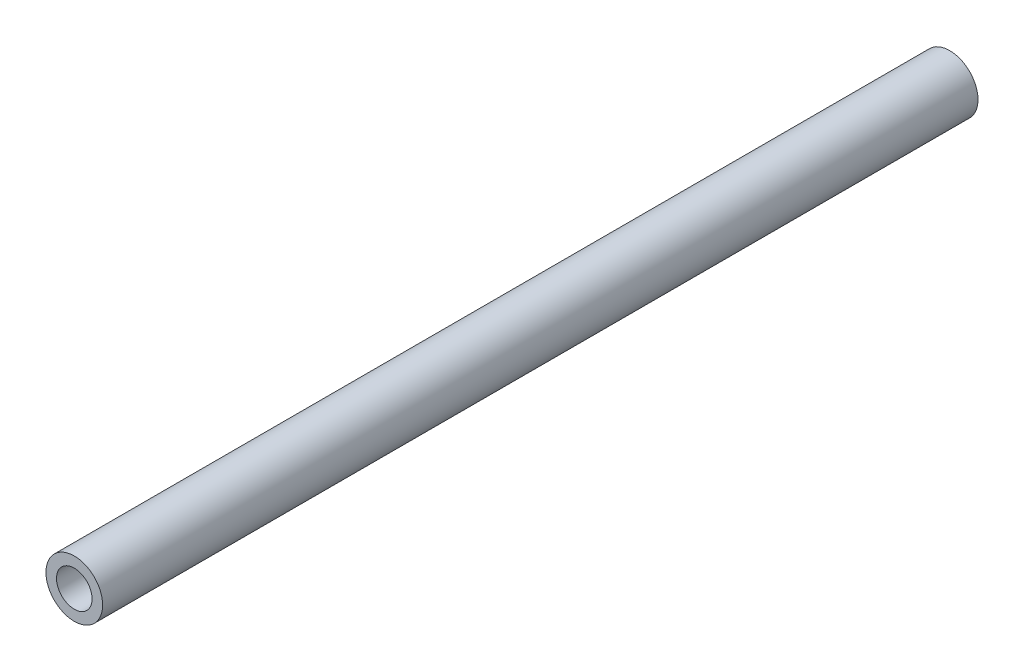
SolidWorks part; units mm, degrees
ref_plane "Plan de face" through (0, 0, 0) normal (0, 0, 1) x (1, 0, 0)
ref_plane "Plan de dessus" through (0, 0, 0) normal (0, 1, 0) x (1, 0, 0)
ref_plane "Plan de droite" through (0, 0, 0) normal (1, 0, 0) x (0, 0, -1)
sketch "Esquisse1" plane through (0, 0, 0) normal (0, 0, 1) x (1, 0, 0)
  circle A0 centre (0, 0) radius 6.475
  dimension "D1" = 12.95
extrude "Boss.-Extru.1" add sketch "Esquisse1" along normal blind 200
sketch "Esquisse2" plane through (0, 0, 0) normal (0, 0, -1) x (-1, 0, 0)
  circle A0 centre (0, 0) radius 4.065
  dimension "D1" = 8.13
extrude "Enlèv. mat.-Extru.1" cut sketch "Esquisse2" against normal through all
